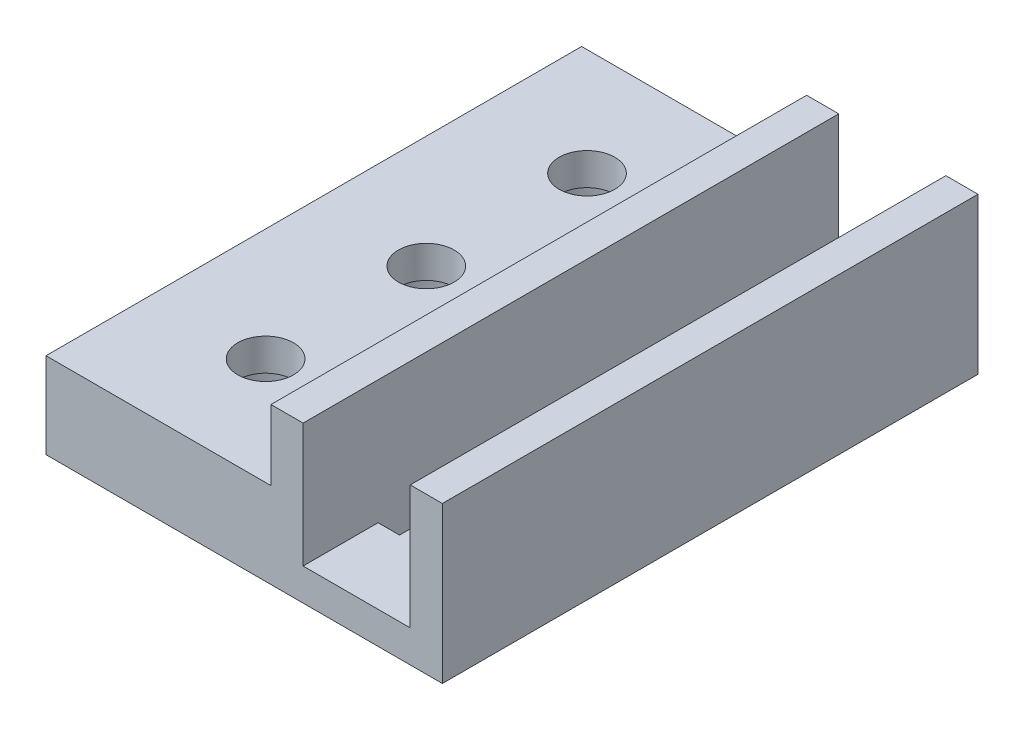
SolidWorks part; units mm, degrees
ref_plane "Front Plane" through (0, 0, 0) normal (0, 0, 1) x (1, 0, 0)
ref_plane "Top Plane" through (0, 0, 0) normal (0, 1, 0) x (1, 0, 0)
ref_plane "Right Plane" through (0, 0, 0) normal (1, 0, 0) x (0, 0, -1)
sketch "Sketch1" plane through (0, 0, 0) normal (0, 1, 0) x (1, 0, 0)
  line L0 (0, 25) -> (0, -25) construction
  line L1 (-10.5, 25) -> (10.5, 25)
  line L2 (-10.5, 25) -> (-10.5, -25)
  line L3 (-10.5, -25) -> (10.5, -25)
  line L4 (10.5, 25) -> (10.5, -25)
  line L5 (-10.5, 25) -> (10.5, -25) construction
  line L6 (-10.5, -25) -> (10.5, 25) construction
  line L7 (-10.5, 0) -> (10.5, 0) construction
  circle A0 centre (0, -15) radius 2.6
  circle A1 centre (0, 0) radius 2.6
  circle A3 centre (0, 15) radius 2.6
  point P0 (0, 0)
  dimension "D4" = 5.2
  dimension "D1" = 21
  dimension "D2" = 50
  dimension "D3" = 10
extrude "Boss-Extrude1" add sketch "Sketch1" along normal blind 8
sketch "Sketch2" plane through (0, 0, 0) normal (0, -1, 0) x (1, 0, 0)
  circle A0 centre (0, 0) radius 5.5
  circle A1 centre (0, 15) radius 5.5
  circle A2 centre (0, -15) radius 5.5
  dimension "D1" = 11
extrude "Cut-Extrude1" cut sketch "Sketch2" against normal blind 5
sketch "Sketch3" plane through (0, 0, 25) normal (0, 0, 1) x (1, 0, 0)
  line L1 (10.5, 0) -> (26.5, 0)
  line L2 (10.5, 0) -> (10.5, 14.5554)
  line L3 (10.5, 14.5554) -> (26.5, 14.5554)
  line L4 (26.5, 0) -> (26.5, 14.5554)
  line L5 (13.5, 14.5554) -> (23.5, 14.5554)
  line L6 (13.5, 14.5554) -> (13.5, 3)
  line L7 (13.5, 3) -> (23.5, 3)
  line L8 (23.5, 14.5554) -> (23.5, 3)
  point P9 (13.5, 8.7777)
  point P10 (18.5, 3)
  line M10 (10.5, 0) -> (10.5, 8)
  dimension "D1" = 16
  dimension "D2" = 3
  dimension "D3" = 3
  dimension "D4" = 3
extrude "Boss-Extrude2" add sketch "Sketch3" against normal up to surface (50 mm away) contours L3 L8 L7 L6 L2 L1 L4 M10 up to face at (0, 4, -25)
sketch "Sketch4" plane through (0, 3, 0) normal (0, 1, 0) x (1, 0, 0)
  line L0 (18.5, 25) -> (18.5, -25) construction
  line L1 (23.5, 25) -> (13.5, 25) construction
  line L2 (13.5, -25) -> (23.5, -25) construction
  line L3 (13.5, 0) -> (23.5, 0) construction
  line L4 (13.5, 25) -> (13.5, -25) construction
  line L5 (23.5, 25) -> (23.5, -25) construction
  line L11 (13.5, 25) -> (13.5, -25) construction
  line L16 (13.5, -13) -> (15.5, -13)
  line L17 (13.5, -13) -> (13.5, -18)
  line L18 (13.5, -18) -> (15.5, -18)
  line L19 (15.5, -13) -> (15.5, -18)
  line L20 (13.5, 18) -> (15.5, 18)
  line L21 (15.5, 13) -> (15.5, 18)
  line L22 (13.5, 13) -> (15.5, 13)
  line L23 (13.5, 13) -> (13.5, 18)
  line L24 (21.5, 2.5) -> (21.5, -2.5)
  line L25 (13.5, 2.5) -> (15.5, 2.5)
  line L26 (13.5, 2.5) -> (13.5, -2.5)
  line L27 (13.5, -2.5) -> (15.5, -2.5)
  line L28 (15.5, 2.5) -> (15.5, -2.5)
  line L29 (23.5, -2.5) -> (21.5, -2.5)
  line L30 (23.5, 2.5) -> (23.5, -2.5)
  line L31 (23.5, 2.5) -> (21.5, 2.5)
  line L32 (23.5, 13) -> (23.5, 18)
  line L33 (23.5, 13) -> (21.5, 13)
  line L34 (21.5, 13) -> (21.5, 18)
  line L35 (23.5, 18) -> (21.5, 18)
  line L36 (21.5, -13) -> (21.5, -18)
  line L37 (23.5, -18) -> (21.5, -18)
  line L38 (23.5, -13) -> (23.5, -18)
  line L39 (23.5, -13) -> (21.5, -13)
  point P26 (13.5, 6.4237)
  point P27 (13.5, 0)
  dimension "D1" = 2
  dimension "D2" = 5
  dimension "D3" = 7
extrude "Cut-Extrude2" cut sketch "Sketch4" against normal up to next
